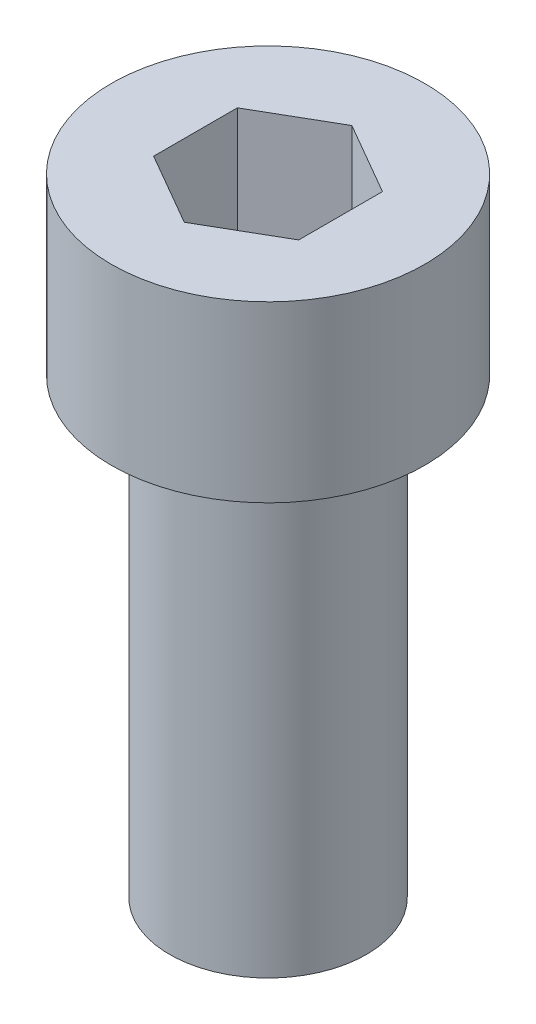
SolidWorks part; units mm, degrees
ref_plane "Front Plane" through (0, 0, 0) normal (0, 0, 1) x (1, 0, 0)
ref_plane "Top Plane" through (0, 0, 0) normal (0, 1, 0) x (1, 0, 0)
ref_plane "Right Plane" through (0, 0, 0) normal (1, 0, 0) x (0, 0, -1)
sketch "Sketch1" plane through (0, 0, 0) normal (0, 1, 0) x (1, 0, 0)
  circle A0 centre (184.7145, -125.2443) radius 2.7
  dimension "D1" = 5.4
extrude "Boss-Extrude1" add sketch "Sketch1" against normal blind 3
sketch "Sketch2" plane through (0, -3, 0) normal (0, -1, 0) x (1, 0, 0)
  circle A0 centre (184.7145, 125.2443) radius 1.6963
extrude "Boss-Extrude2" add sketch "Sketch2" along normal blind 7.8
sketch "Sketch3" plane through (0, 0, 0) normal (0, 1, 0) x (1, 0, 0)
  line L1 (184.7145, -123.8009) -> (183.4645, -124.5226)
  line L2 (183.4645, -124.5226) -> (183.4645, -125.966)
  line L3 (183.4645, -125.966) -> (184.7145, -126.6877)
  line L4 (184.7145, -126.6877) -> (185.9645, -125.966)
  line L5 (185.9645, -125.966) -> (185.9645, -124.5226)
  line L6 (185.9645, -124.5226) -> (184.7145, -123.8009)
  circle A0 centre (184.7145, -125.2443) radius 1.25 construction
  dimension "D1" = 2.5
extrude "Cut-Extrude1" cut sketch "Sketch3" against normal blind 2
